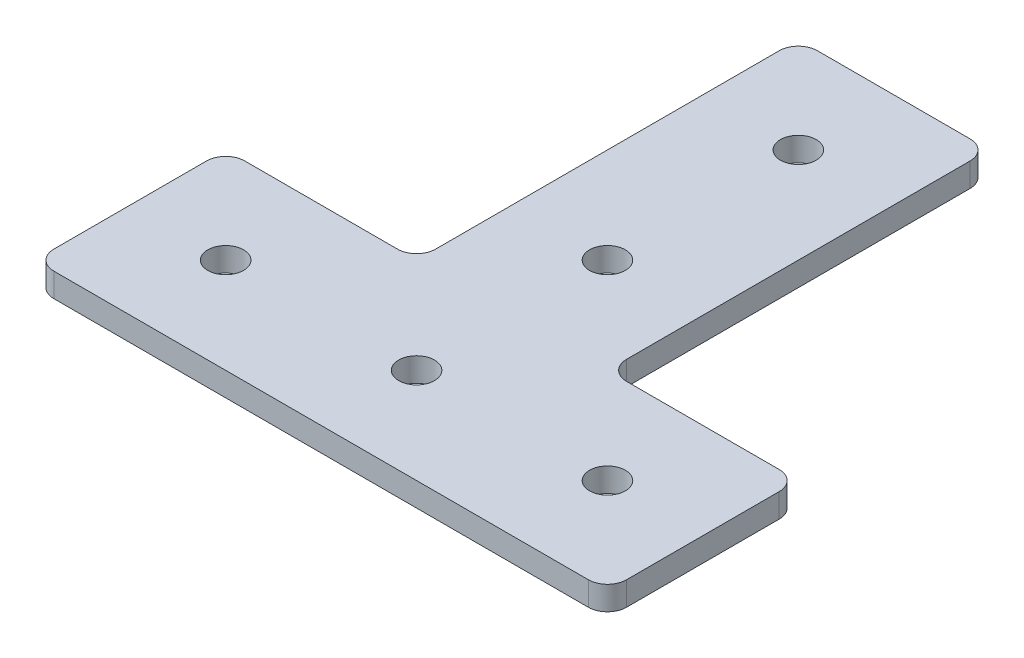
SolidWorks part; units mm, degrees
material "3.0205 (EN-AW 1200)"
ref_plane "Front Plane" through (0, 0, 0) normal (0, 0, 1) x (1, 0, 0)
ref_plane "Top Plane" through (0, 0, 0) normal (0, 1, 0) x (1, 0, 0)
ref_plane "Right Plane" through (0, 0, 0) normal (1, 0, 0) x (0, 0, -1)
sketch "Sketch1" plane through (0, 0, 0) normal (0, 1, 0) x (1, 0, 0)
  line L0 (18.7205, 17.4957) -> (39.0405, 17.4957)
  line L1 (-32.0795, 17.4957) -> (-11.7595, 17.4957)
  line L2 (-34.6195, 14.9557) -> (-34.6195, -5.3643)
  line L3 (-32.0795, -7.9043) -> (39.0405, -7.9043)
  line L4 (41.5805, 14.9557) -> (41.5805, -5.3643)
  line L10 (-9.2195, 20.0357) -> (-9.2195, 65.7557)
  line L11 (-6.6795, 68.2957) -> (13.6405, 68.2957)
  line L12 (16.1805, 20.0357) -> (16.1805, 65.7557)
  circle A0 centre (3.4805, 4.7957) radius 2.3813
  circle A1 centre (-21.9195, 4.7957) radius 2.3813
  circle A2 centre (28.8805, 4.7957) radius 2.3813
  circle A3 centre (3.4805, 30.1957) radius 2.3813
  circle A4 centre (3.4805, 55.5957) radius 2.3812
  arc A5 (16.1805, 65.7557) -> (13.6405, 68.2957) centre (13.6405, 65.7557) ccw
  arc A6 (-9.2195, 65.7557) -> (-6.6795, 68.2957) centre (-6.6795, 65.7557) cw
  arc A7 (-11.7595, 17.4957) -> (-9.2195, 20.0357) centre (-11.7595, 20.0357) ccw
  arc A8 (16.1805, 20.0357) -> (18.7205, 17.4957) centre (18.7205, 20.0357) ccw
  arc A9 (39.0405, 17.4957) -> (41.5805, 14.9557) centre (39.0405, 14.9557) cw
  arc A10 (41.5805, -5.3643) -> (39.0405, -7.9043) centre (39.0405, -5.3643) cw
  arc A11 (-32.0795, -7.9043) -> (-34.6195, -5.3643) centre (-32.0795, -5.3643) cw
  arc A12 (-34.6195, 14.9557) -> (-32.0795, 17.4957) centre (-32.0795, 14.9557) cw
  point P20 (16.1805, 68.2957)
  point P23 (-9.2195, 68.2957)
  point P28 (16.1805, 17.4957)
  point P31 (41.5805, 17.4957)
  point P34 (41.5805, -7.9043)
  point P37 (-34.6195, -7.9043)
  dimension "D6" = 4.7625
  dimension "D7" = 12.7
  dimension "D8" = 12.7
  dimension "D9" = 4.7625
  dimension "D10" = 4.7625
  dimension "D11" = 12.7
  dimension "D12" = 25.4
  dimension "D13" = 25.4
  dimension "D14" = 12.7
  dimension "D15" = 4.7625
  dimension "D16" = 25.4
  dimension "D17" = 12.7
  dimension "D18" = 4.7625
  dimension "D19" = 25.4
  dimension "D20" = 2.54
  dimension "D1" = 76.2
  dimension "D2" = 25.4
  dimension "D3" = 50.8
  dimension "D4" = 25.4
  dimension "D5" = 25.4
extrude "Boss-Extrude1" add sketch "Sketch1" along normal blind 3.175
